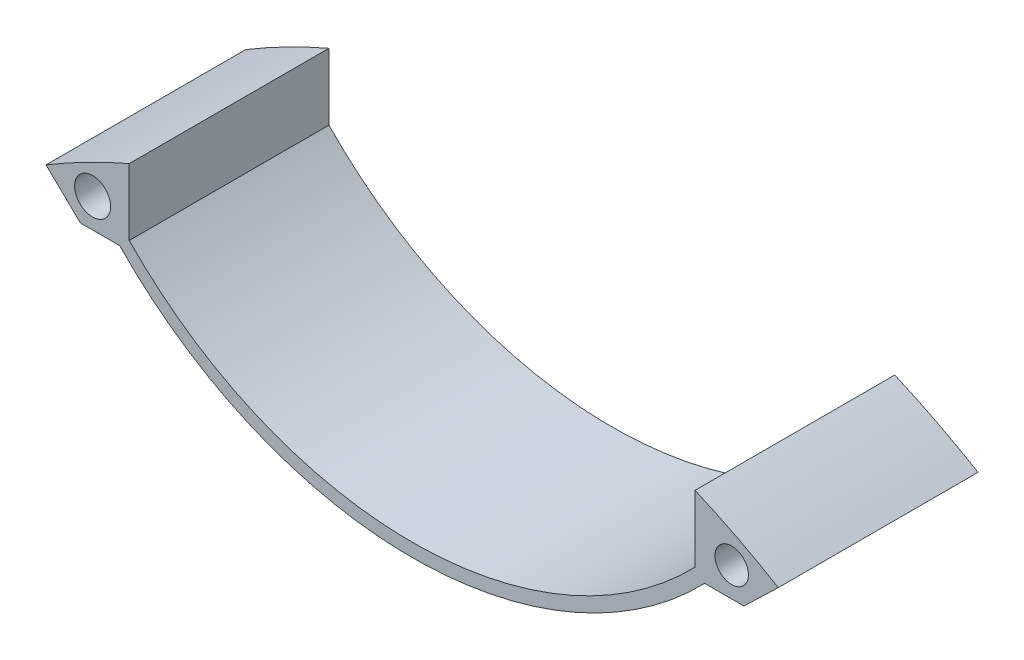
SolidWorks part; units mm, degrees
ref_plane "Front Plane" through (0, 0, 0) normal (0, 0, 1) x (1, 0, 0)
ref_plane "Top Plane" through (0, 0, 0) normal (0, 1, 0) x (1, 0, 0)
ref_plane "Right Plane" through (0, 0, 0) normal (1, 0, 0) x (0, 0, -1)
sketch "Sketch1" plane through (0, 0, 0) normal (0, 0, 1) x (1, 0, 0)
  line L0 (0, 0) -> (0, -15.2176) construction
  line L1 (-42.5, -8.8025) -> (-42.5, -18.8025)
  line L2 (-42.5, -18.8025) -> (42.5, -18.8025) construction
  line L3 (42.5, -18.8025) -> (42.5, -8.8025)
  line L4 (-55, -15.2176) -> (55, -15.2176) construction
  line L5 (-48, -15.8025) -> (48, -15.8025) construction
  line L6 (0, -36.8025) -> (0, -18.8025) construction
  line L7 (0, -15.2176) -> (0, -15.8025) construction
  line L8 (0, -15.8025) -> (0, -18.8025) construction
  line L9 (0, -36.8025) -> (0, -107) construction
  line L10 (-43.9365, -20.1941) -> (-49.8317, -20.1941)
  line L11 (-49.8317, -20.1941) -> (-55, -15.2176)
  line L12 (43.9365, -20.1941) -> (49.8317, -20.1941)
  line L13 (49.8317, -20.1941) -> (55, -15.2176)
  circle A0 centre (0, -107) radius 107 construction
  arc A1 (-42.5, -8.8025) -> (-55, -15.2176) centre (0, -107) ccw
  arc A2 (42.5, -8.8025) -> (55, -15.2176) centre (0, -107) cw
  circle A3 centre (-48, -15.8025) radius 2.703
  circle A4 centre (48, -15.8025) radius 2.5106
  arc A5 (-42.5, -18.8025) -> (42.5, -18.8025) centre (0, 22.3711) ccw
  arc A6 (-43.9365, -20.1941) -> (43.9365, -20.1941) centre (0, 22.3711) ccw
  dimension "D1" = 214
  dimension "D7" = 18
  dimension "D2" = 85
  dimension "D3" = 110
  dimension "D4" = 10
  dimension "D5" = 96
  dimension "D6" = 3
  dimension "D8" = 2
extrude "Boss-Extrude1" add sketch "Sketch1" along normal blind 30
